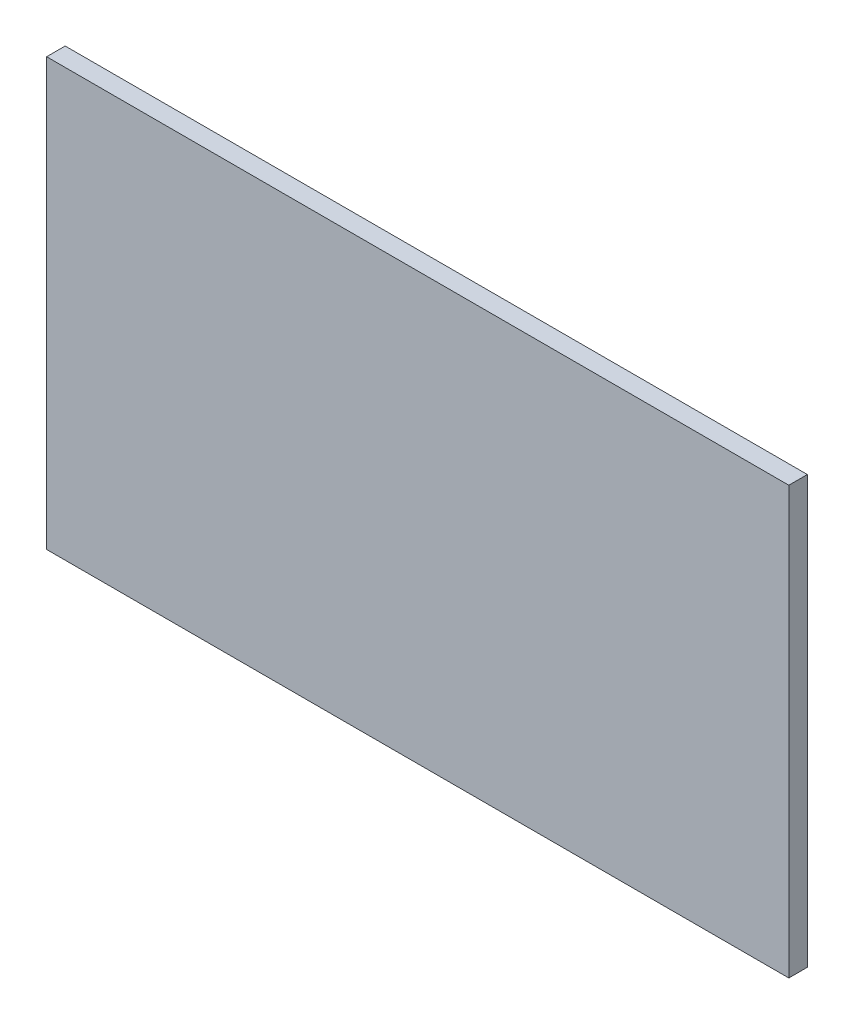
SolidWorks part; units mm, degrees
material "Teck"
ref_plane "Plan de face" through (0, 0, 0) normal (0, 0, 1) x (1, 0, 0)
ref_plane "Plan de dessus" through (0, 0, 0) normal (0, 1, 0) x (1, 0, 0)
ref_plane "Plan de droite" through (0, 0, 0) normal (1, 0, 0) x (0, 0, -1)
sketch "facadeanterieure" plane through (0, 0, 0) normal (0, 0, 1) x (1, 0, 0)
  line L1 (-400, -230) -> (400, -230)
  line L2 (-400, -230) -> (-400, 230)
  line L3 (-400, 230) -> (400, 230)
  line L4 (400, -230) -> (400, 230)
  line L5 (-400, -230) -> (400, 230) construction
  line L6 (-400, 230) -> (400, -230) construction
  point P0 (0, 0)
  dimension "D1" = 800
  dimension "D2" = 460
extrude "Boss.-Extru.1" add sketch "facadeanterieure" along normal blind 20
